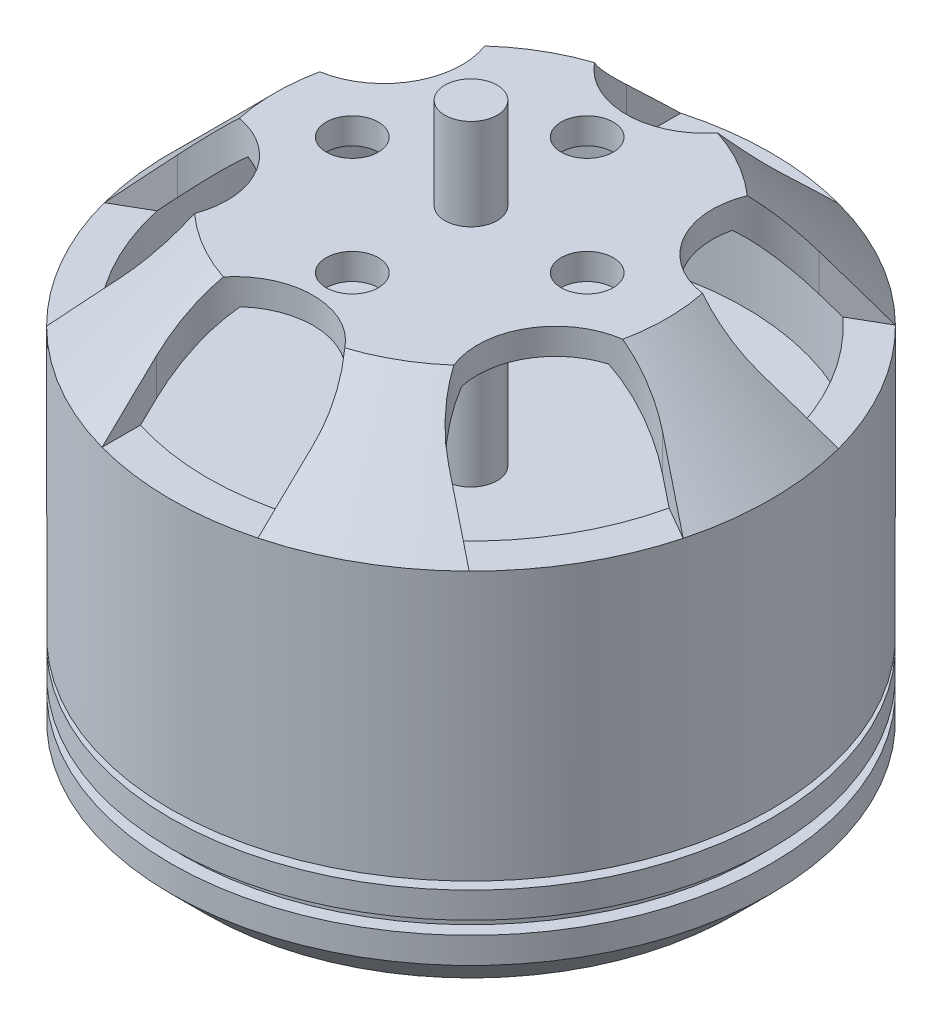
SolidWorks part; units mm, degrees
ref_plane "Front Plane" through (0, 0, 0) normal (0, 0, 1) x (1, 0, 0)
ref_plane "Top Plane" through (0, 0, 0) normal (0, 1, 0) x (1, 0, 0)
ref_plane "Right Plane" through (0, 0, 0) normal (1, 0, 0) x (0, 0, -1)
sketch "Sketch1" plane through (0, 0, 0) normal (0, 0, 1) x (1, 0, 0)
  line L1 (0.049, -2.3622) -> (1.049, -2.3622)
  line L2 (1.049, -2.3622) -> (1.049, -0.5622)
  line L3 (1.049, -0.5622) -> (10.1348, -0.5622)
  line L4 (10.1348, -0.5622) -> (11.549, 0.852)
  line L6 (11.549, 13.9378) -> (7.549, 17.9378)
  line L7 (7.549, 17.9378) -> (1.049, 17.9378)
  line L8 (1.049, 17.9378) -> (1.049, 21.4378)
  line L9 (1.049, 21.4378) -> (0.049, 21.4378)
  line L11 (0.049, 21.4378) -> (0.049, -2.3622)
  line L12 (2.049, 16.9378) -> (7.1348, 16.9378)
  line L13 (7.1348, 16.9378) -> (10.549, 13.5236)
  line L16 (10.549, 9.3053) -> (1.049, 9.3053)
  line L17 (1.049, 9.3053) -> (1.049, 15.9378)
  line L18 (1.049, 15.9378) -> (2.049, 15.9378)
  line L19 (2.049, 15.9378) -> (2.049, 16.9378)
  line L20 (10.549, 9.3053) -> (10.549, 13.5236)
  line L21 (11.549, 3.652) -> (9.549, 3.652)
  line L22 (9.549, 3.652) -> (9.549, 3.352)
  line L23 (9.549, 3.352) -> (11.549, 3.352)
  line L24 (11.549, 3.352) -> (11.549, 2.352)
  line L25 (11.549, 2.352) -> (11.049, 2.352)
  line L26 (11.049, 2.352) -> (11.049, 1.852)
  line L27 (11.049, 1.852) -> (11.549, 1.852)
  line L28 (11.549, 3.652) -> (11.549, 13.9378)
  line L29 (11.549, 1.852) -> (11.549, 0.852)
  dimension "D1" = 23.8
  dimension "D2" = 3.5
  dimension "D3" = 1
  dimension "D4" = 1
  dimension "D5" = 1.8
  dimension "D6" = 45
  dimension "D8" = 11.5
  dimension "D9" = 2
  dimension "D10" = 1
  dimension "D11" = 1
  dimension "D13" = 1
  dimension "D14" = 1
  dimension "D15" = 1
  dimension "D16" = 4
  dimension "D17" = 0.5
  dimension "D18" = 0.5
  dimension "D19" = 0.3
  dimension "D20" = 2
  dimension "D21" = 1
  dimension "D22" = 1
revolve "Revolve1" add sketch "Sketch1" angle 360 about L11
sketch "Sketch2" plane through (0, 17.9378, 0) normal (0, 1, 0) x (1, 0, 0)
  line L0 (0, 0) -> (0, 9) construction
  line L1 (-3, 9) -> (-3, 17.1856)
  line L2 (-3, 17.1856) -> (3, 17.1856)
  line L3 (3, 17.1856) -> (3, 9)
  line L4 (16.3832, 5.9947) -> (9.2942, 1.9019)
  line L5 (6.2942, 7.0981) -> (13.3832, 11.1909)
  line L6 (13.3832, 11.1909) -> (16.3832, 5.9947)
  line L7 (13.3832, -11.1909) -> (6.2942, -7.0981)
  line L8 (9.2942, -1.9019) -> (16.3832, -5.9947)
  line L9 (16.3832, -5.9947) -> (13.3832, -11.1909)
  line L10 (-3, -17.1856) -> (-3, -9)
  line L11 (3, -9) -> (3, -17.1856)
  line L12 (3, -17.1856) -> (-3, -17.1856)
  line L13 (-16.3832, -5.9947) -> (-9.2942, -1.9019)
  line L14 (-6.2942, -7.0981) -> (-13.3832, -11.1909)
  line L15 (-13.3832, -11.1909) -> (-16.3832, -5.9947)
  line L16 (-13.3832, 11.1909) -> (-6.2942, 7.0981)
  line L17 (-9.2942, 1.9019) -> (-16.3832, 5.9947)
  line L18 (-16.3832, 5.9947) -> (-13.3832, 11.1909)
  circle A0 centre (0, 0) radius 4.5 construction
  circle A1 centre (0, 4.5) radius 1
  circle A2 centre (4.5, 0) radius 1
  circle A3 centre (0, -4.5) radius 1
  circle A4 centre (-4.5, 0) radius 1
  arc A5 (-3, 9) -> (3, 9) centre (0, 9) ccw
  arc A6 (6.2942, 7.0981) -> (9.2942, 1.9019) centre (7.7942, 4.5) ccw
  arc A7 (9.2942, -1.9019) -> (6.2942, -7.0981) centre (7.7942, -4.5) ccw
  arc A8 (3, -9) -> (-3, -9) centre (0, -9) ccw
  arc A9 (-6.2942, -7.0981) -> (-9.2942, -1.9019) centre (-7.7942, -4.5) ccw
  arc A10 (-9.2942, 1.9019) -> (-6.2942, 7.0981) centre (-7.7942, 4.5) ccw
  point P15 (0, 0)
  point P45 (0, 0)
  dimension "D1" = 9
  dimension "D3" = 2
  dimension "D5" = 6
  dimension "D2" = 9
  dimension "D4" = 4
  dimension "D6" = 6
extrude "Cut-Extrude1" cut sketch "Sketch2" against normal blind 4
sketch "Sketch3" plane through (0, -0.5622, 0) normal (0, -1, 0) x (1, 0, 0)
  circle A0 centre (0, 0) radius 8 construction
  circle A1 centre (0, 0) radius 6 construction
  circle A2 centre (0, 6) radius 1
  circle A3 centre (6, 0) radius 1
  circle A4 centre (0, -6) radius 1
  circle A5 centre (-6, 0) radius 1
  dimension "D1" = 16
  dimension "D2" = 12
  dimension "D3" = 2
extrude "Cut-Extrude2" cut sketch "Sketch3" against normal blind 3
